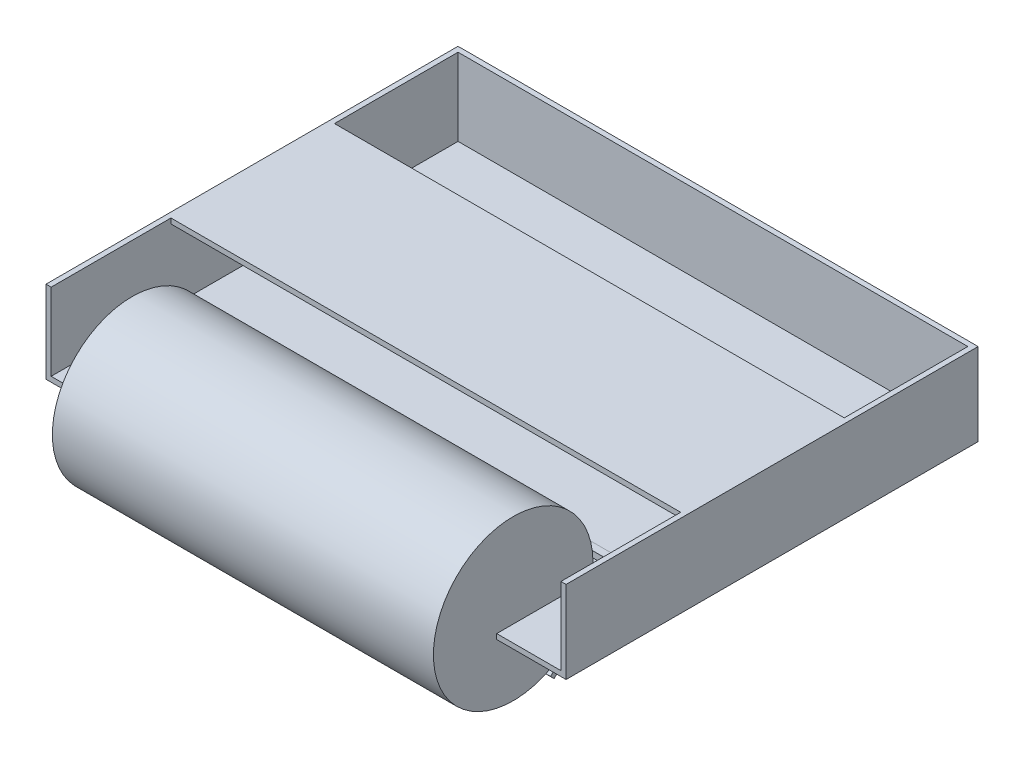
SolidWorks part; units mm, degrees
ref_plane "Front Plane" through (0, 0, 0) normal (0, 0, 1) x (1, 0, 0)
ref_plane "Top Plane" through (0, 0, 0) normal (0, 1, 0) x (1, 0, 0)
ref_plane "Right Plane" through (0, 0, 0) normal (1, 0, 0) x (0, 0, -1)
sketch "Sketch1" plane through (0, 0, 0) normal (0, 1, 0) x (1, 0, 0)
  line L1 (-314.2658, 200) -> (-309.2658, 200)
  line L2 (-314.2658, 200) -> (-314.2658, -200)
  line L3 (-314.2658, -200) -> (-309.2658, -200)
  line L4 (-309.2658, 200) -> (-309.2658, -200)
  dimension "D1" = 400
  dimension "D2" = 5
extrude "Boss-Extrude1" add sketch "Sketch1" along normal blind 80
ref_plane "Plane1" through (-309.2658, 80, -200) normal (0, 0, -1) x (-1, 0, 0)
sketch "Sketch6" plane through (-314.2658, 0, 116.0148) normal (-1, 0, 0) x (0, 1, 0)
  line L1 (20.9551, 316.0466) -> (25.9551, 316.0466)
  line L2 (20.9551, 316.0466) -> (20.9551, -83.9534)
  line L3 (20.9551, -83.9534) -> (25.9551, -83.9534)
  line L4 (25.9551, 316.0466) -> (25.9551, -83.9534)
  dimension "D1" = 400
  dimension "D2" = 5
move or copy body "Body-Move/Copy2" bodies to move or copy 101 copy yes number of copies 1 translate (500, 0, 0)
sketch "Sketch10" plane through (-22.3413, 0, 0) normal (0, 1, 0) x (1, 0, 0)
  line L1 (-288.3825, 200.1128) -> (211.6175, 200.1128)
  line L2 (-288.3825, 200.1128) -> (-288.3825, 195.1128)
  line L3 (-288.3825, 195.1128) -> (211.6175, 195.1128)
  line L4 (211.6175, 200.1128) -> (211.6175, 195.1128)
  dimension "D1" = 500
  dimension "D2" = 5
extrude "Boss-Extrude5" add sketch "Sketch10" along normal blind 80 separate body
sketch "Sketch11" plane through (0, 0, 0) normal (0, 1, 0) x (1, 0, 0)
  line L0 (-309.2658, -200) -> (-309.2658, 200) construction
  line L1 (-309.2658, 195.1128) -> (185.7342, 195.1128)
  line L2 (-309.2658, 195.1128) -> (-309.2658, -200)
  line L3 (-309.2658, -200) -> (185.7342, -200)
  line L4 (185.7342, 195.1128) -> (185.7342, -200)
  line L5 (-310.7239, 195.1128) -> (189.2761, 195.1128) construction
extrude "Boss-Extrude6" add sketch "Sketch11" along normal blind 5
sketch "Sketch12" plane through (0, 8.7868, -129.0555) normal (1, 0, 0) x (0, 0, -1)
  line L0 (-200, 0) -> (-330, -65)
  line L1 (-200, 0) -> (-330, 0)
  line L2 (-200, 0) -> (-200, -65)
  line L3 (-200, -65) -> (-330, -65)
  line L4 (-330, 0) -> (-330, -65)
  line L5 (-330, -65) -> (-200, -6.8185)
  line L6 (-200, 0) -> (-330, -65)
  dimension "D1" = 130
  dimension "D2" = 65
extrude "Extrude-Thin1" add sketch "Sketch12" along normal blind 190 and the other way blind 313.1595 separate body thin contours L5
sketch "Sketch13" plane through (0, 0, 122.4376) normal (1, 0, 0) x (0, 0, -1)
  circle A0 centre (-176.5364, 16.8387) radius 77.5
move or copy body "Body-Move/Copy4" bodies to move or copy 110 copy no rotation origin (0, -29.3928, 134.9285) rotation axis (1, 0, 0) rotation angle 10
move or copy body "Body-Move/Copy5" bodies to move or copy 112 copy no rotation origin (0, -29.3928, 134.9285) rotation axis (1, 0, 0) rotation angle 10
move or copy body "Body-Move/Copy6" bodies to move or copy 113 copy no translate (0, 20.014, -39.9865)
sketch "Sketch15" plane through (0, 0, 0) normal (0, 0, 1) x (1, 0, 0)
  line L0 (-309.2658, 80) -> (-309.2658, 5) construction
  line L1 (-309.2658, 42.5) -> (185.7342, 42.5)
  line L2 (-309.2658, 42.5) -> (-309.2658, 5)
  line L3 (-309.2658, 5) -> (185.7342, 5)
  line L4 (185.7342, 42.5) -> (185.7342, 5)
extrude "Cut-Extrude2" cut sketch "Sketch15" against normal blind 22 and the other way blind 96
sketch "Sketch17" plane through (0, 0, 0) normal (0, 1, 0) x (1, 0, 0)
  line L1 (-246.5906, -83.7319) -> (123.4094, -83.7319)
  line L2 (-246.5906, -83.7319) -> (-246.5906, -283.7319)
  line L3 (-246.5906, -283.7319) -> (123.4094, -283.7319)
  line L4 (123.4094, -83.7319) -> (123.4094, -283.7319)
  dimension "D1" = 370
  dimension "D2" = 200
extrude "Cut-Extrude4" cut sketch "Sketch17" along normal blind 53 and the other way blind 1 contours L2 L1 L4 L3
extrude "Boss-Extrude8" add sketch "Sketch13" along normal blind 370 contours A0
move or copy body "Body-Move/Copy9" bodies to move or copy 124 copy no translate (-247.7027, 0, -116.0943)
sketch "Sketch20" plane through (0, 0, 0) normal (0, 0, 1) x (1, 0, 0)
  line L0 (-313.1595, -57.1606) -> (-313.1595, 41.9747) construction
  line L1 (-313.1595, 0) -> (-246.3224, 0)
  line L2 (-313.1595, 0) -> (-313.1595, -67.8209)
  line L3 (-313.1595, -67.8209) -> (-246.3224, -67.8209)
  line L4 (-246.3224, 0) -> (-246.3224, -67.8209)
  line L5 (-314.2658, 0) -> (-246.5906, 0) construction
extrude "Cut-Extrude7" cut sketch "Sketch20" along normal blind 229
sketch "Sketch21" plane through (0, 0, 0) normal (0, 0, 1) x (1, 0, 0)
  line L0 (123.4094, -1) -> (123.4094, 4.9528) construction
  line L9 (123.4094, 0) -> (197.1963, 0)
  line L10 (123.4094, 0) -> (123.4094, -71.5062)
  line L11 (123.4094, -71.5062) -> (197.1963, -71.5062)
  line L12 (197.1963, 0) -> (197.1963, -71.5062)
  line L13 (-246.5906, 0) -> (123.4094, 0) construction
extrude "Cut-Extrude13" cut sketch "Sketch21" along normal blind 266
sketch "Sketch22" plane through (0, 0, 0) normal (0, 1, 0) x (1, 0, 0)
  line L0 (-309.2658, 195.1128) -> (-309.2658, -200) construction
  line L1 (-309.2658, 75.1128) -> (185.7342, 75.1128)
  line L2 (-309.2658, 75.1128) -> (-309.2658, 70.1128)
  line L3 (-309.2658, 70.1128) -> (185.7342, 70.1128)
  line L4 (185.7342, 75.1128) -> (185.7342, 70.1128)
  line L5 (185.7342, -200) -> (185.7342, 195.1128) construction
  line L6 (185.7342, 195.1128) -> (-309.2658, 195.1128) construction
  line L7 (-309.2658, 195.1128) -> (185.7342, 195.1128) construction
  dimension "D1" = 120
  dimension "D2" = 125
extrude "Boss-Extrude11" add sketch "Sketch22" along normal blind 80
sketch "Sketch24" plane through (0, 0, 0) normal (0, 1, 0) x (1, 0, 0)
  line L1 (-309.2658, 70.1128) -> (185.7342, 70.1128)
  line L2 (-309.2658, 70.1128) -> (-309.2658, -83.6833)
  line L3 (-309.2658, -83.6833) -> (185.7342, -83.6833)
  line L4 (185.7342, 70.1128) -> (185.7342, -83.6833)
extrude "Boss-Extrude12" add sketch "Sketch24" along normal blind 5 from offset 75
